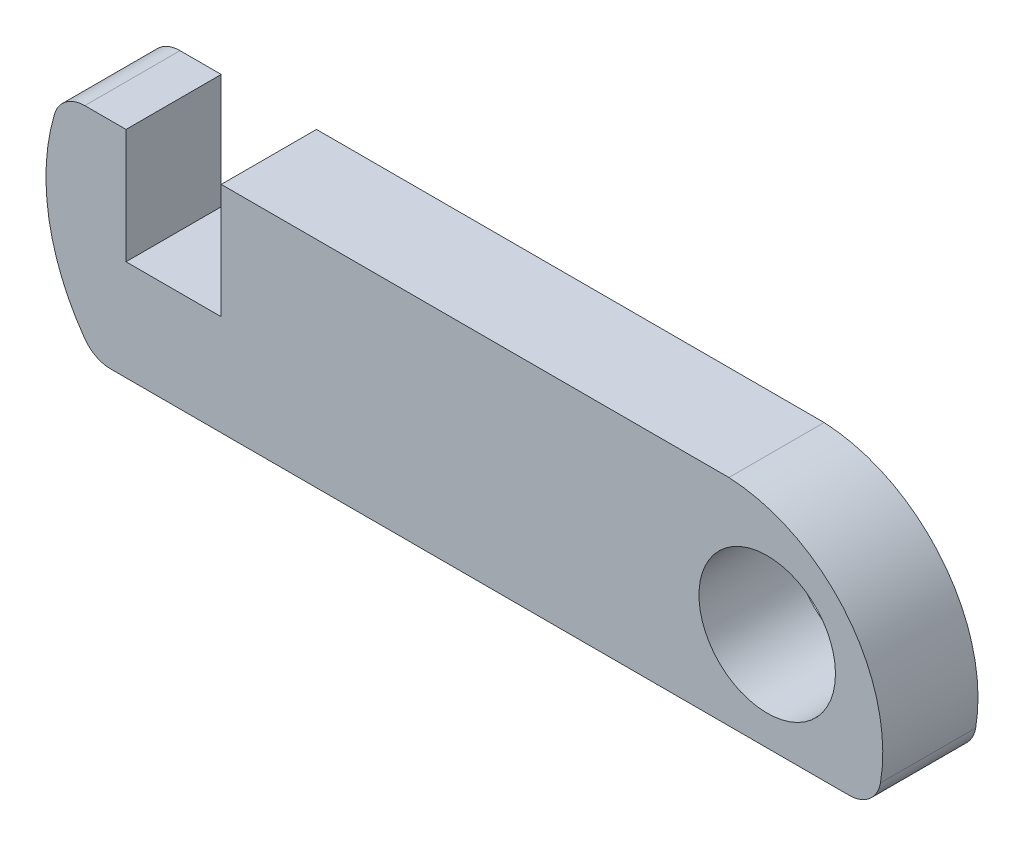
SolidWorks part; units mm, degrees
ref_plane "Front Plane" through (0, 0, 0) normal (0, 0, 1) x (1, 0, 0)
ref_plane "Top Plane" through (0, 0, 0) normal (0, 1, 0) x (1, 0, 0)
ref_plane "Right Plane" through (0, 0, 0) normal (1, 0, 0) x (0, 0, -1)
sketch "Sketch2" plane through (0, 0, 0) normal (0, 0, 1) x (1, 0, 0)
  line L0 (5, 0) -> (20.9934, 0)
  line L1 (0.7021, 0) -> (2, 0)
  line L2 (24.7816, -6.7778) -> (22.8056, -6.7778)
  line L3 (1.5146, -6.7778) -> (22.8056, -6.7778)
  line L6 (2, 0) -> (2, -3.6111)
  line L7 (2, -3.6111) -> (5, -3.6111)
  line L8 (5, 0) -> (5, -3.6111)
  arc A0 (0.7022, -6.3608) -> (-0.2574, -0.7183) centre (6.0034, -2.5565) cw
  arc A1 (0.7021, 0) -> (-0.2574, -0.7183) centre (0.7021, -1) ccw
  arc A2 (0.7022, -6.3608) -> (1.5146, -6.7778) centre (1.5146, -5.7778) ccw
  arc A3 (20.505, 0) -> (25.7672, -5.947) centre (20.7492, -5.0855) cw
  circle A4 centre (22.2, -3.6778) radius 2.15
  arc A5 (25.7672, -5.947) -> (24.7816, -6.7778) centre (24.7816, -5.7778) cw
  dimension "D2" = 1
  dimension "D3" = 1
  dimension "D4" = 4.3
  dimension "D5" = 17.2
  dimension "D6" = 3.1
  dimension "D7" = 1
  dimension "D1" = 3
extrude "Boss-Extrude1" add sketch "Sketch2" along normal blind 3 contours A5 A3 L0 L8 L7 L6 L1 A1 A0 A2 L3 L2 A4
